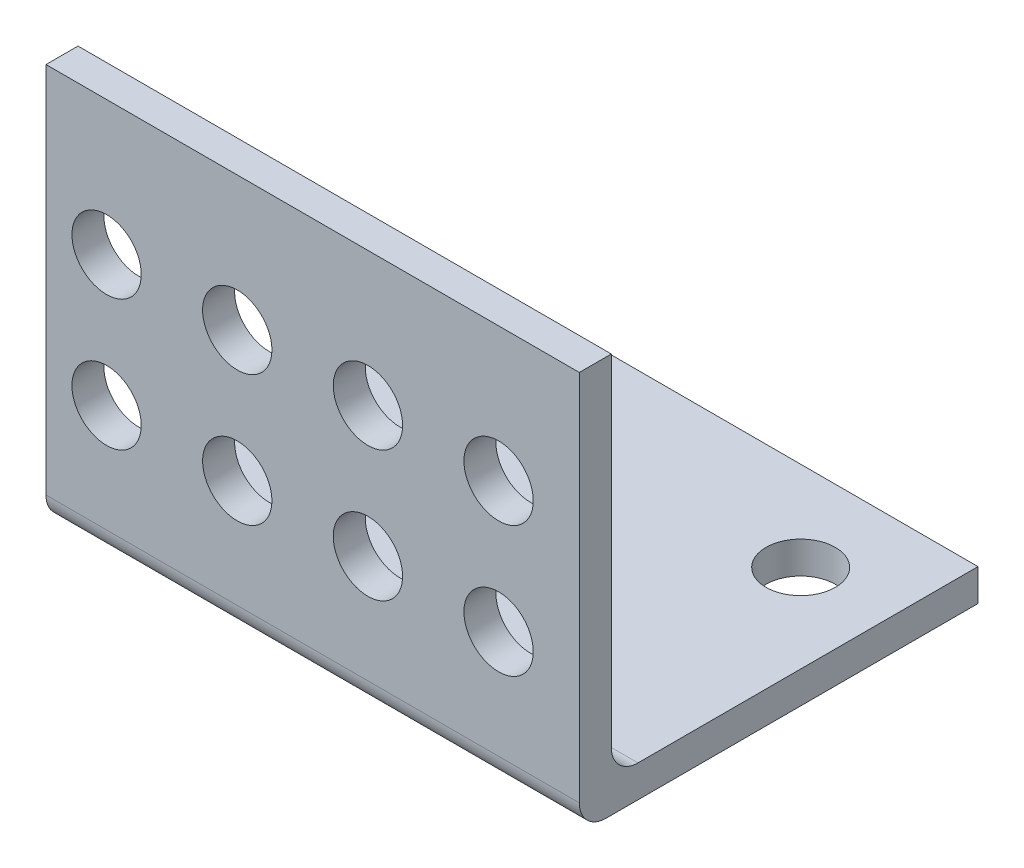
SolidWorks part; units mm, degrees
ref_plane "Front Plane" through (0, 0, 0) normal (0, 0, 1) x (1, 0, 0)
ref_plane "Top Plane" through (0, 0, 0) normal (0, 1, 0) x (1, 0, 0)
ref_plane "Right Plane" through (0, 0, 0) normal (1, 0, 0) x (0, 0, -1)
sketch "Sketch1" plane through (0, 0, 0) normal (0, 0, 1) x (1, 0, 0)
  line L0 (-40.8158, -17.9492) -> (-0.7858, -17.9492)
  line L2 (-0.7858, -17.9492) -> (-0.7858, 12.0108)
  line L3 (-40.8158, 12.0108) -> (-0.7858, 12.0108)
  line L4 (-40.8158, 12.0108) -> (-40.8158, -17.9492)
  circle A0 centre (-35.4558, 1.9408) radius 2.6
  circle A1 centre (-25.6558, 1.9408) radius 2.6
  circle A2 centre (-15.8558, 1.9408) radius 2.6
  circle A3 centre (-6.0558, 1.9408) radius 2.6
  circle A4 centre (-6.0558, -7.8592) radius 2.6
  circle A5 centre (-15.8558, -7.8592) radius 2.6
  circle A6 centre (-25.6558, -7.8592) radius 2.6
  circle A7 centre (-35.4558, -7.8592) radius 2.6
sketch "Sketch3" plane through (0, 0, 0) normal (1, 0, 0) x (0, 0, -1)
  line L0 (2, -17.9492) -> (29.9, -17.9492)
  line L1 (0, 12.0108) -> (0, -17.9492) construction
  line L2 (0, -17.9492) -> (0, 12.0108) construction
  line L3 (0, 12.0108) -> (0, -15.9492)
  line L4 (0, 12.0108) -> (2.4, 12.0108)
  line L5 (2.4, 12.0108) -> (2.4, -13.5492)
  line L6 (4.4, -15.5492) -> (29.9, -15.5492)
  line L7 (29.9, -15.5492) -> (29.9, -17.9492)
  arc A0 (0, -15.9492) -> (2, -17.9492) centre (2, -15.9492) ccw
  arc A1 (2.4, -13.5492) -> (4.4, -15.5492) centre (4.4, -13.5492) ccw
  point P10 (0, -17.9492)
  point P14 (0, -17.9492)
  dimension "D1" = 2
  dimension "D2" = 2
extrude "Boss-Extrude2" add sketch "Sketch3" against normal blind 40
extrude "Cut-Extrude4" cut sketch "Sketch1" against normal blind 40 contours A1 | A0 | A6 | A5 | A4 | A3 | A2 | A7
sketch "Sketch5" plane through (0, -15.5492, 0) normal (0, 1, 0) x (1, 0, 0)
  circle A0 centre (-33.4, 23.2) radius 2.6
  circle A1 centre (-6.6, 23.2) radius 2.6
  circle A2 centre (-20, 13.2) radius 2.6
extrude "Cut-Extrude5" cut sketch "Sketch5" against normal blind 40
